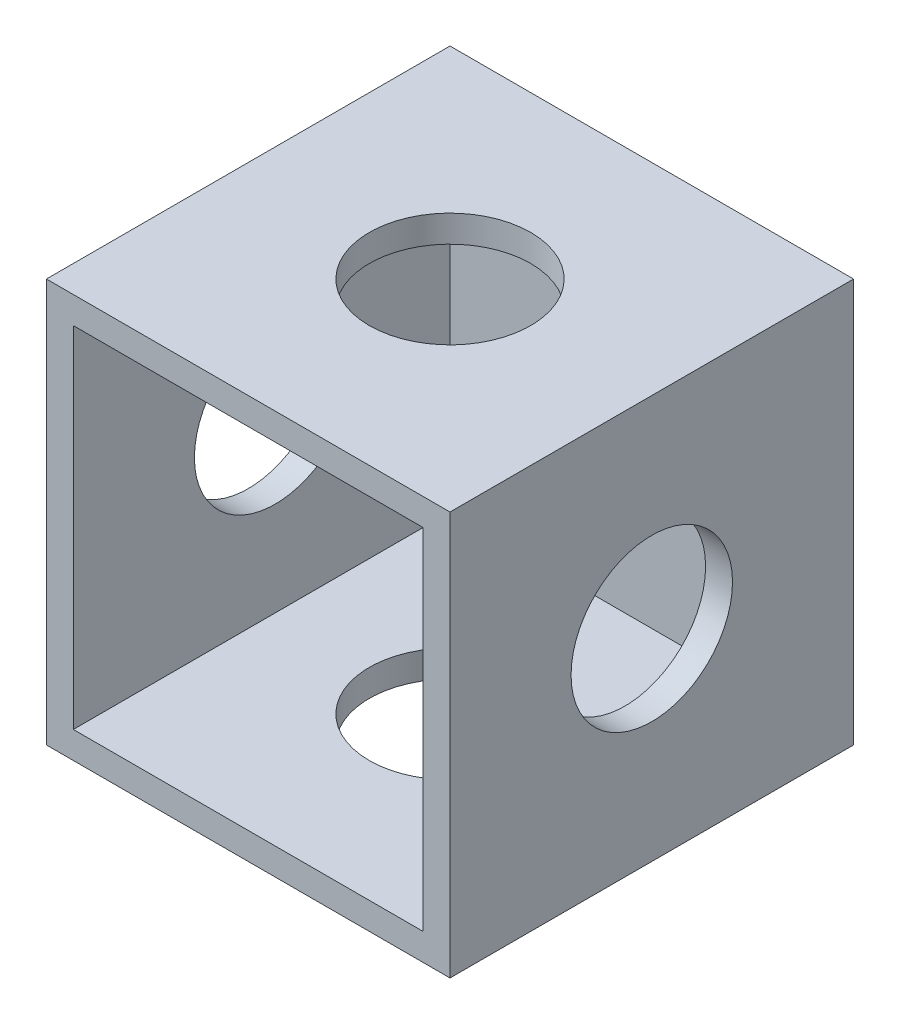
SolidWorks part; units mm, degrees
ref_plane "Front Plane" through (0, 0, 0) normal (1, 0, 0) x (0, 1, 0)
ref_plane "Top Plane" through (0, 0, 0) normal (0, 0, 1) x (0, 1, 0)
ref_plane "Right Plane" through (0, 0, 0) normal (0, 1, 0) x (-1, 0, 0)
sketch "Sketch1" plane through (0, 0, 0) normal (0, 0, 1) x (0, 1, 0)
  line L0 (-15, -15) -> (15, 15) construction
  line L1 (-15, -15) -> (15, -15)
  line L2 (-15, -15) -> (-15, 15)
  line L3 (-15, 15) -> (15, 15)
  line L4 (15, -15) -> (15, 15)
  line L5 (-15, 15) -> (15, -15) construction
  dimension "D1" = 30
  dimension "D2" = 30
extrude "Boss-Extrude1" add sketch "Sketch1" along normal blind 30
shell "Shell1" thickness 2
sketch "Sketch2" plane through (0, 15, 0) normal (0, 1, 0) x (-1, 0, 0)
  line L0 (-15, 30) -> (15, 0) construction
  line L1 (15, 30) -> (-15, 0) construction
  circle A0 centre (0, 15) radius 6
  point P10 (0, 0)
  point P11 (0, 15)
  dimension "D1" = 12
extrude "Cut-Extrude1" cut sketch "Sketch2" against normal blind 40
sketch "Sketch3" plane through (15, 0, 0) normal (1, 0, 0) x (0, 1, 0)
  line L0 (-15, 30) -> (15, 0) construction
  circle A0 centre (0, 15) radius 6
  point P6 (0, 0)
  dimension "D1" = 12
extrude "Cut-Extrude2" cut sketch "Sketch3" against normal blind 40
